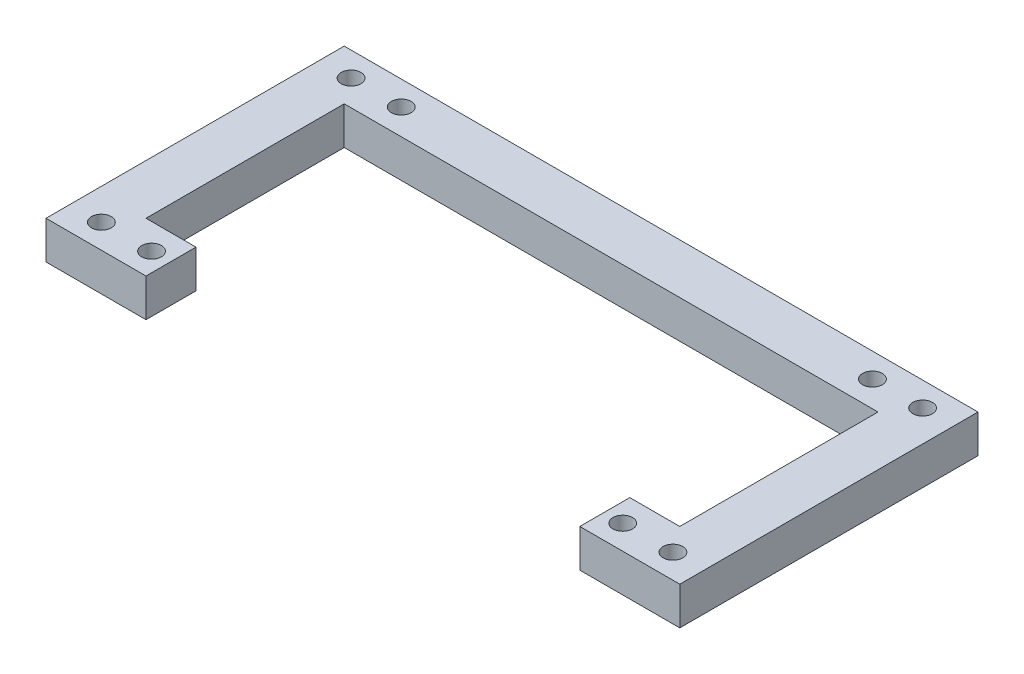
SolidWorks part; units mm, degrees
ref_plane "Front Plane" through (0, 0, 0) normal (0, 0, 1) x (1, 0, 0)
ref_plane "Top Plane" through (0, 0, 0) normal (0, 1, 0) x (1, 0, 0)
ref_plane "Right Plane" through (0, 0, 0) normal (1, 0, 0) x (0, 0, -1)
sketch "Sketch1" plane through (0, 0, 0) normal (0, 1, 0) x (1, 0, 0)
  line L0 (181.4198, 36.9979) -> (75.1552, 36.9979) construction
  line L1 (75.1552, 11.9979) -> (83.5372, 11.9979)
  line L2 (75.1552, 11.9979) -> (75.1552, 61.9979)
  line L3 (75.1552, 61.9979) -> (83.5372, 61.9979)
  line L4 (83.5372, 11.9979) -> (83.5372, 61.9979)
  line L5 (83.5372, 61.9979) -> (91.9192, 61.9979)
  line L6 (83.5372, 61.9979) -> (83.5372, 53.6159)
  line L7 (83.5372, 53.6159) -> (91.9192, 53.6159)
  line L8 (167.7876, 16.0648) -> (186.7138, 16.0648) construction
  line L9 (83.5372, 11.9979) -> (91.9192, 11.9979)
  line L10 (83.5372, 11.9979) -> (83.5372, 20.3799)
  line L11 (83.5372, 20.3799) -> (91.9192, 20.3799)
  line L12 (91.9192, 11.9979) -> (91.9192, 20.3799)
  line L13 (75.1552, 61.9979) -> (181.4198, 61.9979)
  line L17 (181.4198, 61.9979) -> (173.0378, 61.9979)
  line L18 (181.4198, 61.9979) -> (181.4198, 11.9979)
  line L19 (181.4198, 11.9979) -> (173.0378, 11.9979)
  line L20 (173.0378, 61.9979) -> (173.0378, 11.9979)
  line L21 (173.0378, 61.9979) -> (164.6558, 61.9979)
  line L22 (173.0378, 61.9979) -> (173.0378, 53.6159)
  line L23 (173.0378, 53.6159) -> (164.6558, 53.6159)
  line L25 (173.0378, 11.9979) -> (164.6558, 11.9979)
  line L26 (173.0378, 11.9979) -> (173.0378, 20.3799)
  line L27 (173.0378, 20.3799) -> (164.6558, 20.3799)
  line L28 (164.6558, 11.9979) -> (164.6558, 20.3799)
  line L29 (128.2875, 61.9979) -> (128.2875, -9.1774) construction
  line L30 (164.6558, 53.6159) -> (91.9192, 53.6159)
  circle A0 centre (167.7876, 57.931) radius 1.651
  circle A1 centre (167.7876, 16.0648) radius 1.651
  circle A2 centre (88.7875, 16.0648) radius 1.651
  circle A3 centre (88.7875, 57.931) radius 1.651
  circle A4 centre (176.2028, 16.0648) radius 1.651
  circle A5 centre (80.3722, 16.0648) radius 1.651
  circle A6 centre (80.3722, 57.931) radius 1.651
  circle A7 centre (176.2028, 57.931) radius 1.651
  point P32 (91.9192, 16.1889)
  point P34 (88.7875, 57.931)
  point P35 (88.7875, 16.0648)
  dimension "D15" = 3.302
  dimension "D16" = 3.1342
  dimension "D6" = 79.0001
  dimension "D18" = 3.302
  dimension "D2" = 47.9153
  dimension "D1" = 8.382
  dimension "D3" = 50
  dimension "D4" = 8.382
  dimension "D5" = 50
  dimension "D7" = 8.382
  dimension "D8" = 8.382
  dimension "D9" = 8.382
  dimension "D10" = 8.382
  dimension "D11" = 8.382
  dimension "D12" = 8.382
  dimension "D13" = 8.382
  dimension "D14" = 8.382
  dimension "D17" = 3.1317
extrude "Boss-Extrude1" add sketch "Sketch1" along normal blind 6.35
